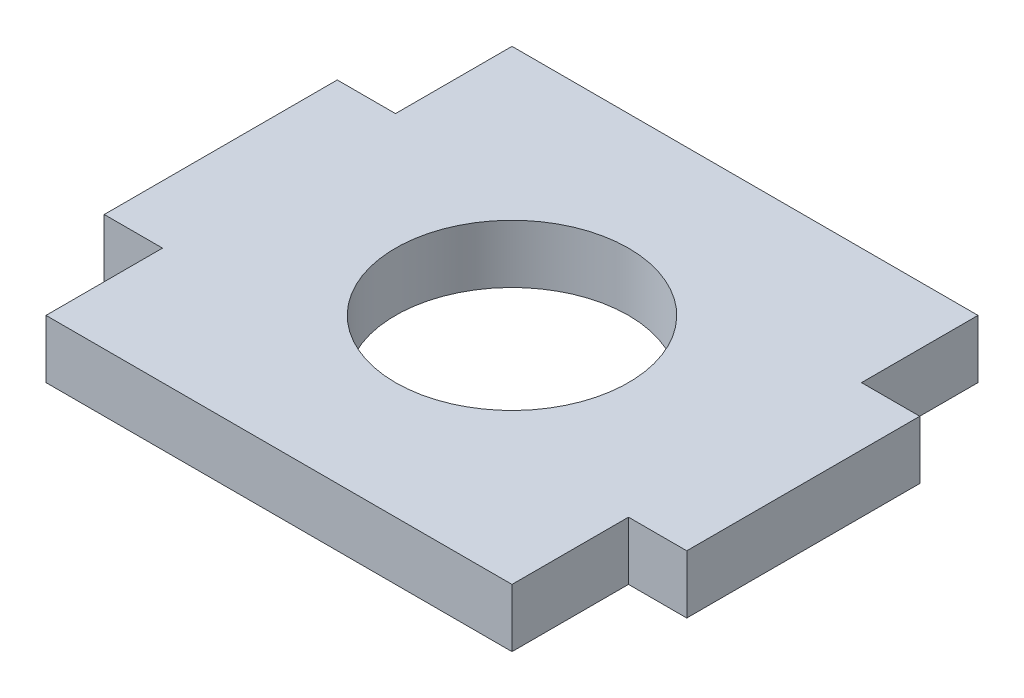
SolidWorks part; units mm, degrees
material "6061-T6 (SS)"
ref_plane "Front Plane" through (0, 0, 0) normal (0, 0, 1) x (1, 0, 0)
ref_plane "Top Plane" through (0, 0, 0) normal (0, 1, 0) x (1, 0, 0)
ref_plane "Right Plane" through (0, 0, 0) normal (1, 0, 0) x (0, 0, -1)
sketch "Sketch1" plane through (0, 0, 0) normal (0, 1, 0) x (1, 0, 0)
  line L0 (-12.7, 6.35) -> (-12.7, 12.7)
  line L1 (12.7, -12.7) -> (-12.7, -12.7)
  line L2 (12.7, -12.7) -> (12.7, -6.35)
  line L3 (12.7, 12.7) -> (-12.7, 12.7)
  line L4 (-12.7, -12.7) -> (-12.7, -6.35)
  line L5 (12.7, -12.7) -> (-12.7, 12.7) construction
  line L6 (12.7, 12.7) -> (-12.7, -12.7) construction
  line L7 (-12.7, 6.35) -> (-15.875, 6.35)
  line L9 (-12.7, -6.35) -> (-15.875, -6.35)
  line L10 (-15.875, 6.35) -> (-15.875, -6.35)
  line L11 (12.7, 6.35) -> (15.875, 6.35)
  line L13 (12.7, -6.35) -> (15.875, -6.35)
  line L14 (15.875, 6.35) -> (15.875, -6.35)
  line L15 (12.7, 6.35) -> (12.7, 12.7)
  point P0 (0, 0)
  dimension "D1" = 6.35
  dimension "D2" = 25.4
  dimension "D3" = 3.175
  dimension "D4" = 25.4
  dimension "D5" = 12.7
extrude "Boss-Extrude1" add sketch "Sketch1" along normal blind 3.175
sketch "Sketch2" plane through (0, 3.175, 0) normal (0, 1, 0) x (1, 0, 0)
  circle A0 centre (0, 0) radius 6.35
  dimension "D1" = 12.7
extrude "Cut-Extrude1" cut sketch "Sketch2" against normal through all
